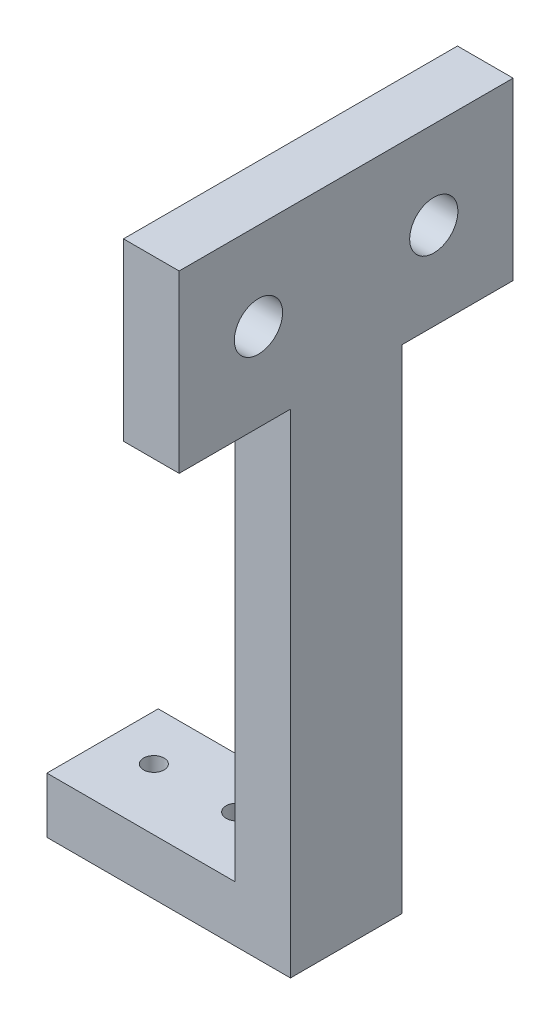
SolidWorks part; units mm, degrees
material "PLA Yellow"
ref_plane "Front Plane" through (0, 0, 0) normal (0, 0, 1) x (1, 0, 0)
ref_plane "Top Plane" through (0, 0, 0) normal (0, 1, 0) x (1, 0, 0)
ref_plane "Right Plane" through (0, 0, 0) normal (1, 0, 0) x (0, 0, -1)
sketch "Sketch1" plane through (0, 0, 0) normal (0, 0, 1) x (1, 0, 0)
  line L0 (-13.8933, 0) -> (13.8933, 0)
  line L10 (13.8933, 76.2) -> (7.5433, 76.2)
  line L11 (7.5433, 76.2) -> (7.5433, 6.35)
  line L12 (7.5433, 6.35) -> (-13.8933, 6.35)
  line L13 (-13.8933, 6.35) -> (-13.8933, 0)
  line L14 (13.8933, 76.2) -> (13.8933, 0)
  point P6 (0, 0)
  dimension "D1" = 27.7866
  dimension "D2" = 76.2
  dimension "D3" = 6.35
  dimension "D4" = 6.35
extrude "Boss-Extrude1" add sketch "Sketch1" along normal mid plane 12.7
sketch "Sketch2" plane through (7.5433, 0, 0) normal (-1, 0, 0) x (0, 0, 1)
  line L0 (6.35, 76.2) -> (-6.35, 76.2) construction
  line L1 (-19.05, 56.2) -> (19.05, 56.2)
  line L2 (-19.05, 56.2) -> (-19.05, 76.2)
  line L3 (-19.05, 76.2) -> (19.05, 76.2)
  line L4 (19.05, 56.2) -> (19.05, 76.2)
  line L5 (-19.05, 56.2) -> (19.05, 76.2) construction
  line L6 (-19.05, 76.2) -> (19.05, 56.2) construction
  point P0 (0, 66.2)
  point P5 (0, 76.2)
  point P8 (0, 76.2)
  dimension "D1" = 20
  dimension "D2" = 38.1
extrude "Boss-Extrude2" add sketch "Sketch2" against normal up to surface (6.35 mm away) up to face at (13.8933, 38.1, 0)
sketch "Sketch3" plane through (0, 6.35, 0) normal (0, 1, 0) x (1, 0, 0)
  arc A0 (0.3802, 1.825) -> (0.3802, -0.525) centre (0.8067, 0.65) ccw construction
  circle A1 centre (-8.6933, 0.65) radius 1.175 construction
  arc A2 (0.3802, 1.825) -> (0.3802, -0.525) centre (0.8067, 0.65) ccw
  circle A3 centre (-8.6933, 0.65) radius 1.175
  circle A4 centre (0.8067, 0.65) radius 1.25
extrude "Cut-Extrude1" cut sketch "Sketch3" against normal through all contours A2 A4 | A3
sketch "Sketch4" plane through (7.5433, 0, 0) normal (-1, 0, 0) x (0, 0, 1)
  line L0 (-10, 66.2) -> (10, 66.2) construction
  line L1 (-19.05, 56.2) -> (19.05, 76.2) construction
  circle A0 centre (-10, 66.2) radius 2.75
  circle A1 centre (10, 66.2) radius 2.75
  point P6 (0, 66.2)
  point P9 (0, 66.2)
  dimension "D1" = 5.5
  dimension "D2" = 20
extrude "Cut-Extrude2" cut sketch "Sketch4" against normal through all
